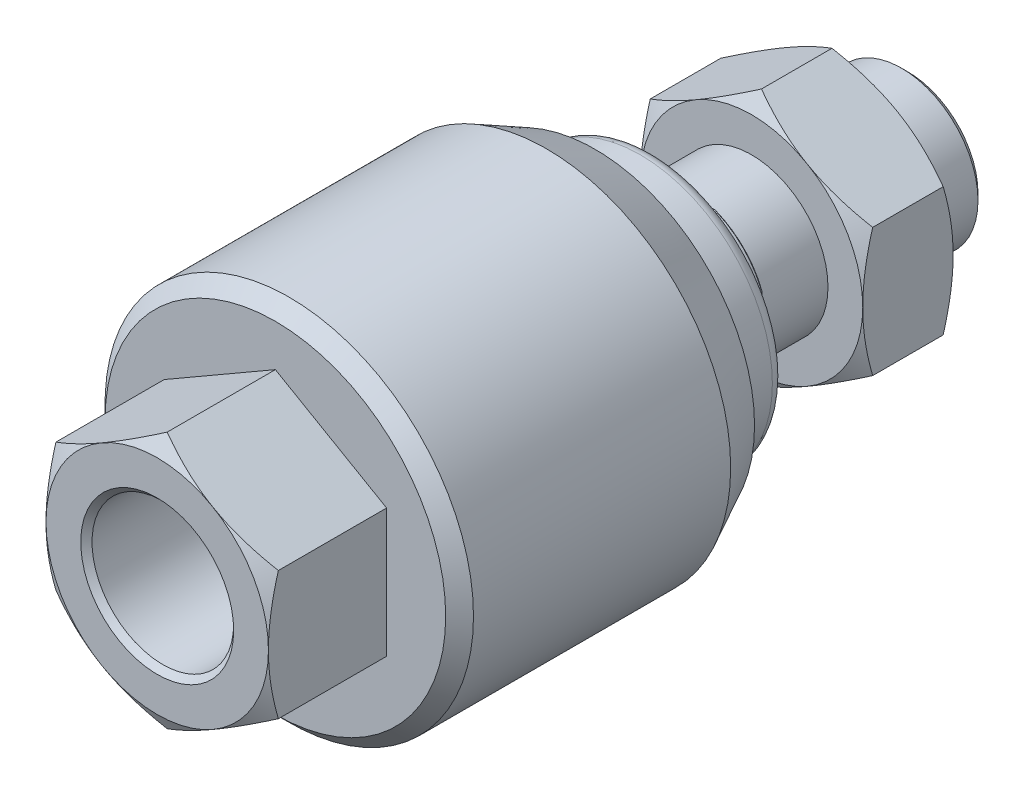
SolidWorks part; units mm, degrees
material "A3钢"
ref_plane "前视基准面" through (0, 0, 0) normal (0, 0, 1) x (1, 0, 0)
ref_plane "上视基准面" through (0, 0, 0) normal (0, 1, 0) x (1, 0, 0)
ref_plane "右视基准面" through (0, 0, 0) normal (1, 0, 0) x (0, 0, -1)
sketch "草图1" plane through (0, 0, 0) normal (1, 0, 0) x (0, 0, -1)
  line L0 (-83, 0) -> (-83, 10.188)
  line L1 (-83, 10.188) -> (-107.188, 10.188)
  line L2 (-107.188, 10.188) -> (-108, 11)
  line L3 (-108, 11) -> (-108, 16)
  line L4 (-108, 16) -> (-106.5709, 18.4752)
  line L5 (-106.5709, 18.4752) -> (-91.6, 18.4752)
  line L6 (-91.6, 18.4752) -> (-91, 19.0752)
  line L7 (-91, 19.0752) -> (-91, 24.5)
  line L8 (-91, 24.5) -> (-89, 26.5)
  line L9 (-89, 26.5) -> (-52, 26.5)
  line L10 (-52, 26.5) -> (-45, 22.9333)
  line L11 (-45, 22.9333) -> (-45, 10.5)
  line L12 (-45, 10.5) -> (-38.5, 10.5)
  line L13 (-38.5, 10.5) -> (-38.5, 11.8)
  line L14 (-38.5, 11.8) -> (-38.3, 12)
  line L15 (-38.3, 12) -> (-32.2, 12)
  line L16 (-32.2, 12) -> (-32, 11.8)
  line L17 (-32, 11.8) -> (-32, 11)
  line L18 (-32, 11) -> (-0.92, 11)
  line L19 (-0.92, 11) -> (0, 10.08)
  line L20 (0, 10.08) -> (0, 0)
  line L21 (0, 0) -> (-83, 0)
  line L22 (0, 0) -> (-108, 0) construction
revolve "旋转1" add sketch "草图1" angle 360 about L22
cosmetic thread "装饰螺纹线1" parameters "D1"=32, "D2"=20.16
cosmetic thread "装饰螺纹线2" parameters "D1"=25, "D2"=22
ref_plane "基准面1" through (0, 0, 32) normal (0, 0, -1) x (-1, 0, 0)
sketch "草图2" plane through (0, 0, 32) normal (0, 0, -1) x (-1, 0, 0)
  line L0 (-22, -11) -> (22, -11)
  line L1 (22, -11) -> (22, 11)
  line L2 (22, 11) -> (-22, 11)
  line L3 (-22, 11) -> (-22, -11)
  circle A0 centre (0, 0) radius 33
extrude "切除-拉伸1" cut sketch "草图2" against normal blind 6.5
ref_plane "基准面2" through (0, 0, 32) normal (0, 0, -1) x (-1, 0, 0)
sketch "草图3" plane through (0, 0, 32) normal (0, 0, -1) x (-1, 0, 0)
  line L0 (-11, -22) -> (11, -22)
  line L1 (11, -22) -> (11, 22)
  line L2 (11, 22) -> (-11, 22)
  line L3 (-11, 22) -> (-11, -22)
  circle A0 centre (0, 0) radius 33
extrude "切除-拉伸2" cut sketch "草图3" against normal blind 6.5
sketch "草图4" plane through (0, 0, 0) normal (1, 0, 0) x (0, 0, -1)
  line L0 (-45, 19) -> (-45, 10.5)
  line L1 (-45, 10.5) -> (-38.5, 10.5)
  line L2 (-38.5, 10.5) -> (-38.5, 11.8)
  line L3 (-38.5, 11.8) -> (-36.7263, 16.4189)
  line L4 (-38.5, 19) -> (-45, 19)
  line L5 (50, 0) -> (-50, 0) construction
  arc A0 (-36.7263, 16.4189) -> (-38.5, 19) centre (-38.5, 17.1) ccw
revolve "旋转2" add sketch "草图4" angle 360 about L5
ref_plane "基准面3" through (0, 0, 108) normal (0, 0, 1) x (1, 0, 0)
sketch "草图5" plane through (0, 0, 108) normal (0, 0, 1) x (1, 0, 0)
  line L0 (0, -18.4752) -> (16, -9.2376)
  line L1 (16, -9.2376) -> (16, 9.2376)
  line L2 (16, 9.2376) -> (0, 18.4752)
  line L3 (0, 18.4752) -> (-16, 9.2376)
  line L4 (-16, 9.2376) -> (-16, -9.2376)
  line L5 (-16, -9.2376) -> (0, -18.4752)
  circle A0 centre (0, 0) radius 32
extrude "切除-拉伸3" cut sketch "草图5" against normal blind 17
sketch "草图6" plane through (0, 0, 0) normal (1, 0, 0) x (0, 0, -1)
  line L0 (-22.5, 16) -> (-22.5, 11)
  line L1 (-22.5, 11) -> (-21.688, 10.188)
  line L2 (-21.688, 10.188) -> (-10.312, 10.188)
  line L3 (-10.312, 10.188) -> (-9.5, 11)
  line L4 (-9.5, 11) -> (-9.5, 16)
  line L5 (-9.5, 16) -> (-10.9291, 18.4752)
  line L6 (-10.9291, 18.4752) -> (-21.0709, 18.4752)
  line L7 (-21.0709, 18.4752) -> (-22.5, 16)
  line L8 (-9.5, 0) -> (-22.5, 0) construction
revolve "旋转3" add sketch "草图6" angle 360 about L8
ref_plane "基准面4" through (0, 0, 9.5) normal (0, 0, -1) x (-1, 0, 0)
sketch "草图7" plane through (0, 0, 9.5) normal (0, 0, -1) x (-1, 0, 0)
  line L0 (0, -18.4752) -> (16, -9.2376)
  line L1 (16, -9.2376) -> (16, 9.2376)
  line L2 (16, 9.2376) -> (0, 18.4752)
  line L3 (0, 18.4752) -> (-16, 9.2376)
  line L4 (-16, 9.2376) -> (-16, -9.2376)
  line L5 (-16, -9.2376) -> (0, -18.4752)
  circle A0 centre (0, 0) radius 32
extrude "切除-拉伸4" cut sketch "草图7" against normal blind 13
